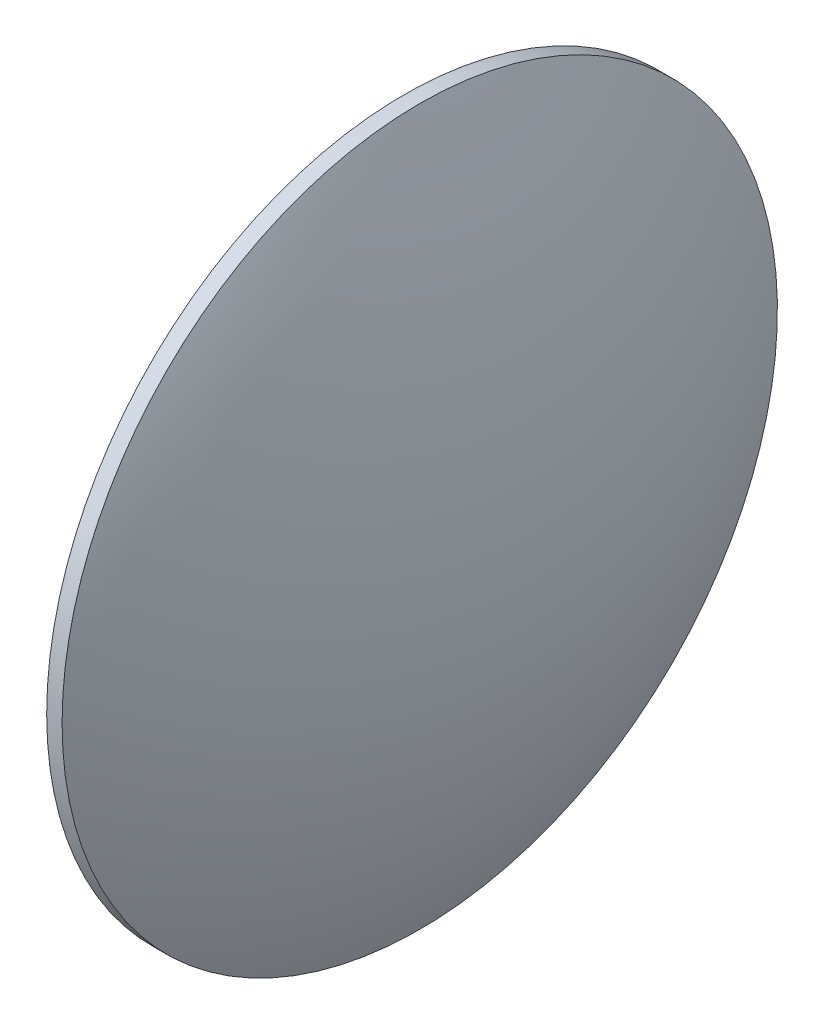
SolidWorks part; units mm, degrees
ref_plane "前视基准面" through (0, 0, 0) normal (0, 0, 1) x (1, 0, 0)
ref_plane "上视基准面" through (0, 0, 0) normal (0, 1, 0) x (1, 0, 0)
ref_plane "右视基准面" through (0, 0, 0) normal (1, 0, 0) x (0, 0, -1)
sketch "草图1" plane through (0, 0, 0) normal (0, 0, 1) x (1, 0, 0)
  line L0 (187.8163, -255.6057) -> (205.9154, -255.6057) construction
  line L1 (191.8595, -255.6057) -> (191.8595, -233.1057)
  line L2 (191.8595, -233.1057) -> (192.8295, -233.1057)
  line L3 (197.9595, -255.6057) -> (191.8595, -255.6057)
  arc A0 (197.9595, -255.6057) -> (192.8295, -233.1057) centre (146.0524, -255.6057) ccw
revolve "旋转1" add sketch "草图1" angle 360 about L0
